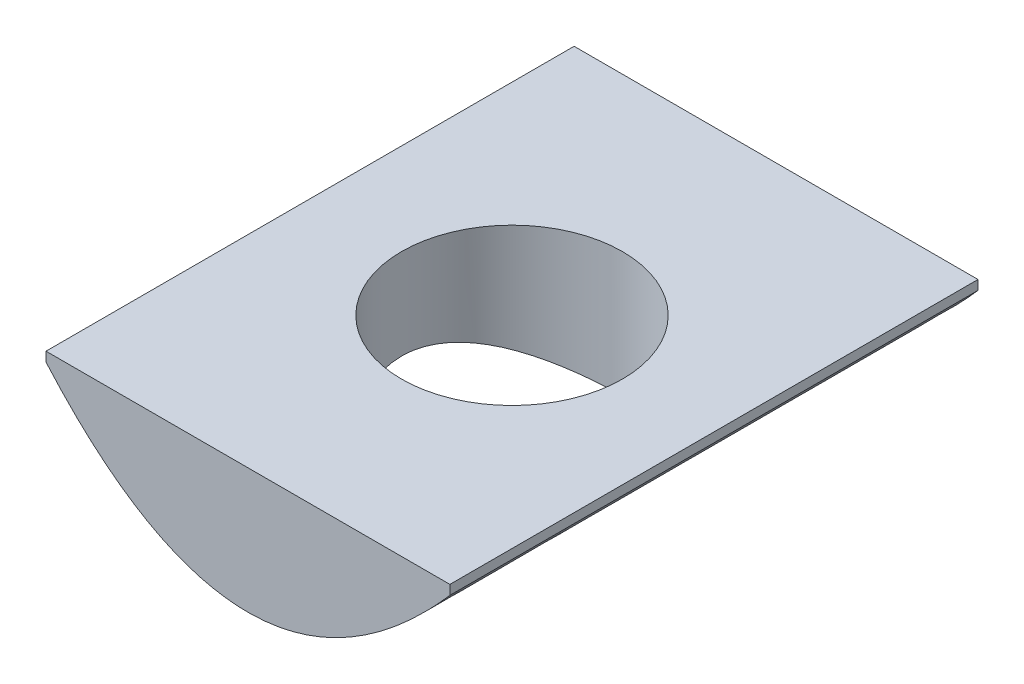
SolidWorks part; units mm, degrees
material "1060 Alloy"
ref_plane "Front Plane" through (0, 0, 0) normal (0, 0, 1) x (1, 0, 0)
ref_plane "Top Plane" through (0, 0, 0) normal (0, 1, 0) x (1, 0, 0)
ref_plane "Right Plane" through (0, 0, 0) normal (1, 0, 0) x (0, 0, -1)
sketch "Sketch1" plane through (0, 0, 0) normal (0, 0, 1) x (1, 0, 0)
  line L0 (-5.4102, 0) -> (5.4102, 0)
  line L1 (-5.4102, 0) -> (-5.4102, -0.254)
  line L2 (5.4102, 0) -> (5.4102, -0.254)
  spline S0 degree 2 poles (-5.4102, -0.254) (0, -6.4516) (5.4102, -0.254) knots 0 0 0 1 1 1
  point P4 (0, 0)
  point P5 (0, -3.3528)
  dimension "D6" = 12.8582
  dimension "D1" = 3.3528
  dimension "D2" = 0.254
  dimension "D3" = 5.4102
  dimension "D4" = 5.4102
  dimension "D5" = 0.254
extrude "Boss-Extrude1" add sketch "Sketch1" along normal blind 14.1478 contours L1 S0 L2 L0
sketch "Sketch2" plane through (0, 0, 0) normal (0, 1, 0) x (1, 0, 0)
  line L0 (5.4102, 0) -> (5.4102, -14.1478) construction
  circle A0 centre (0, -7.0739) radius 2.9591
  point P7 (5.4102, -7.0739)
  dimension "D1" = 5.9182
extrude "Cut-Extrude1" cut sketch "Sketch2" against normal blind 14.1478
